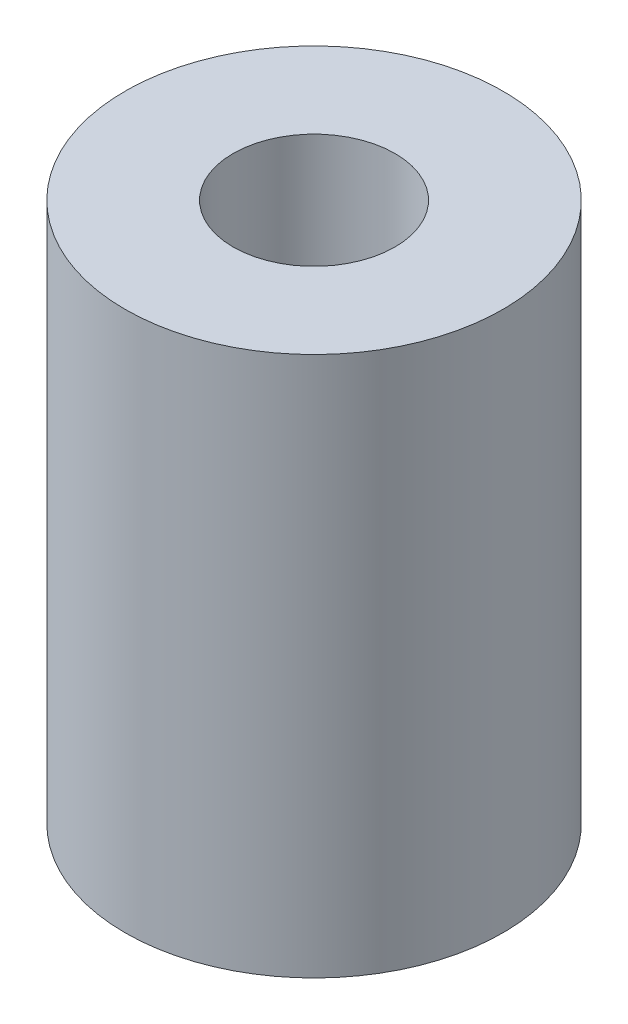
SolidWorks part; units mm, degrees
material "尼龙 101"
ref_plane "前视基准面" through (0, 0, 0) normal (0, 0, 1) x (1, 0, 0)
ref_plane "上视基准面" through (0, 0, 0) normal (0, 1, 0) x (1, 0, 0)
ref_plane "右视基准面" through (0, 0, 0) normal (1, 0, 0) x (0, 0, -1)
sketch "草图1" plane through (0, 0, 0) normal (0, 1, 0) x (1, 0, 0)
  circle A0 centre (0, 0) radius 3.5
  circle A1 centre (0, 0) radius 1.5
  dimension "D1" = 3
  dimension "D2" = 7
extrude "凸台-拉伸1" add sketch "草图1" along normal blind 10
